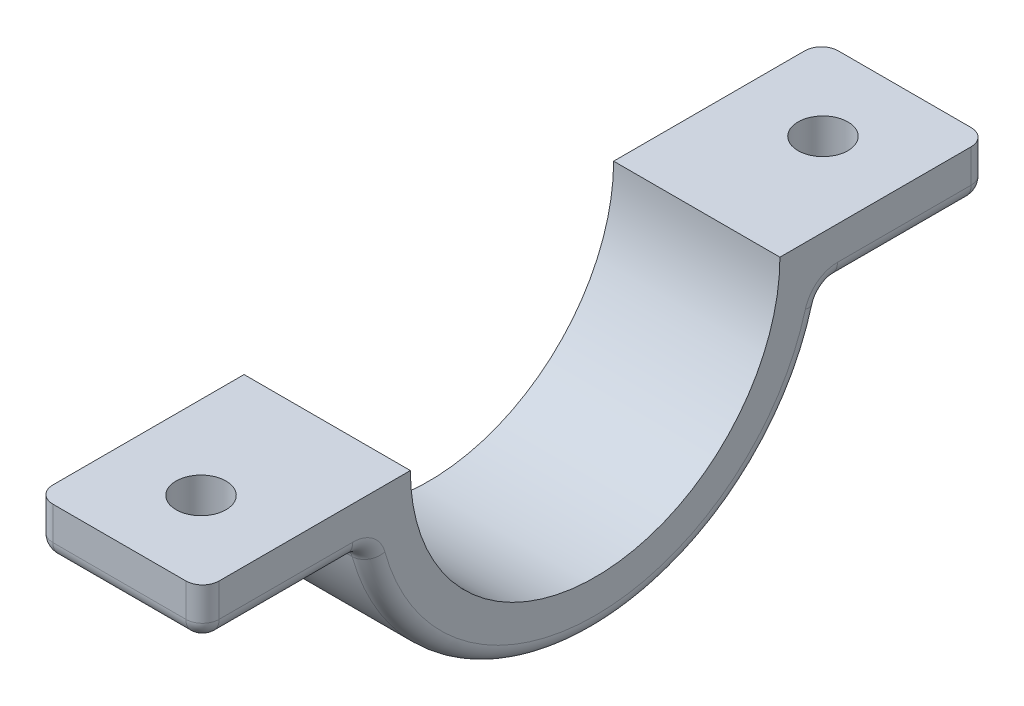
SolidWorks part; units mm, degrees
ref_plane "Front Plane" through (0, 0, 0) normal (0, 0, 1) x (1, 0, 0)
ref_plane "Top Plane" through (0, 0, 0) normal (0, 1, 0) x (1, 0, 0)
ref_plane "Right Plane" through (0, 0, 0) normal (1, 0, 0) x (0, 0, -1)
sketch "Sketch4" plane through (0, 0, 0) normal (1, 0, 0) x (0, 0, -1)
  line L0 (-23.6125, 0) -> (-11.1125, 0)
  line L2 (-23.6125, 0) -> (-23.6125, -3)
  line L3 (-23.6125, -3) -> (-13.7899, -3)
  line L4 (23.6125, 0) -> (23.6125, -3)
  line L5 (13.7899, -3) -> (23.6125, -3)
  line L6 (11.1125, 0) -> (23.6125, 0)
  arc A0 (-11.1125, 0) -> (11.1125, 0) centre (0, 0) ccw
  arc A2 (-13.7899, -3) -> (13.7899, -3) centre (0, 0) ccw
  dimension "D2" = 22.225
  dimension "D1" = 12.5
  dimension "D3" = 12.5
  dimension "D4" = 3
  dimension "D5" = 3
extrude "Clamp Extrude" add sketch "Sketch4" along normal blind 10
sketch "Hole" plane through (0, -3, 0) normal (0, -1, 0) x (1, 0, 0)
  line L2 (10, 23.6125) -> (0, 23.6125) construction
  line L3 (10, 13.7899) -> (0, 13.7899) construction
  line L4 (0, 23.6125) -> (0, 13.7899) construction
  line L5 (10, 23.6125) -> (10, 13.7899) construction
  line L6 (0, 0) -> (10, 0)
  line L7 (0, 13.7899) -> (0, -13.7899) construction
  line L8 (10, -13.7899) -> (10, 13.7899) construction
  circle A0 centre (5, 18.7012) radius 1.5
  circle A1 centre (5, -18.7012) radius 1.5
  dimension "D1" = 3
  dimension "D2" = 9.8226
  dimension "D3" = 4.9113
  dimension "D4" = 10
  dimension "D5" = 5
extrude "Holes Cut-Extrude" cut sketch "Hole" against normal through all contours A0 | A1
fillet "Fillet1" radius 1 14 edges at (10, -3, -18.7012) (0, -3, -18.7012) (10, -14.1125, 0) (0, -14.1125, 0) (0, -1.5, 23.6125) (10, -1.5, 23.6125) (10, -1.5, -23.6125) (0, -1.5, -23.6125) (5, -3, -23.6125) (5, -3, -13.7899) (5, -3, 13.7899) (10, -3, 18.7012) (5, -3, 23.6125) (0, -3, 18.7012)
equation "\"D3@Hole\"=\"D2@Hole\"/2"
equation "\"D5@Hole\"=\"D4@Hole\"/2"
equation "\"D3@Sketch4\"=\"D1@Sketch4\""
